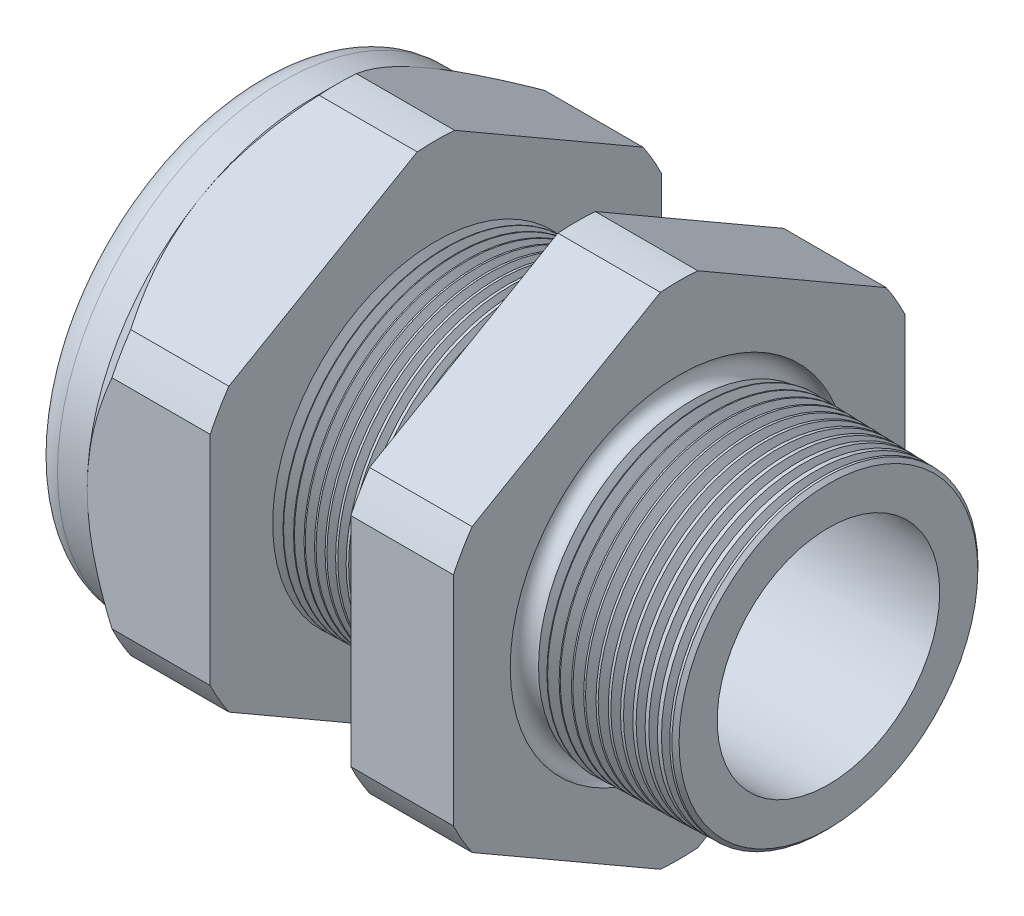
SolidWorks part; units mm, degrees
ref_plane "Front Plane" through (0, 0, 0) normal (0, 0, 1) x (1, 0, 0)
ref_plane "Top Plane" through (0, 0, 0) normal (0, 1, 0) x (1, 0, 0)
ref_plane "Right Plane" through (0, 0, 0) normal (1, 0, 0) x (0, 0, -1)
sketch "Sketch10" plane through (0, 0, 0) normal (0, 0, 1) x (1, 0, 0)
  line L0 (0, 0) -> (-115.3565, 0) construction
  line L1 (-38.862, 9.017) -> (-25.662, 9.017)
  line L2 (3.048, 8.1382) -> (3.048, 11.1862)
  line L3 (-7.874, 11.4722) -> (3.048, 11.1862)
  line L4 (-7.874, 33.02) -> (-7.874, 11.4722)
  line L5 (-7.874, 33.02) -> (-15.374, 33.02)
  line L6 (-15.374, 33.02) -> (-15.374, 11.6686)
  line L7 (-25.662, 11.938) -> (-15.374, 11.6686)
  line L8 (-25.662, 11.938) -> (-25.662, 33.02)
  line L9 (-25.662, 33.02) -> (-34.662, 33.02)
  line L10 (-34.662, 33.02) -> (-34.662, 16.51)
  line L11 (-34.662, 16.51) -> (-38.862, 16.51)
  line L12 (-38.862, 16.51) -> (-38.862, 9.017)
  line L13 (-25.662, 9.017) -> (3.048, 8.1382)
  dimension "D1" = 41.91
  dimension "D2" = 18.034
  dimension "D3" = 1.5
  dimension "D4" = 3.048
  dimension "A" = 23.876
  dimension "D6" = 33.02
  dimension "D8" = 66.04
  dimension "D9" = 4.2
  dimension "D10" = 9
  dimension "D11" = 7.5
  dimension "D" = 10.922
revolve "Revolve2" add sketch "Sketch10" angle 360 about L0
sketch "Sketch12" plane through (-34.662, 0, 0) normal (-1, 0, 0) x (0, 0, 1)
  line L1 (-1.3666, 18.2751) -> (-15.1434, 10.3211)
  line L2 (-16.51, 7.954) -> (-16.51, -7.954)
  line L3 (-15.1434, -10.3211) -> (-1.3666, -18.2751)
  line L4 (1.3666, -18.2751) -> (15.1434, -10.3211)
  line L5 (16.51, -7.954) -> (16.51, 7.954)
  line L6 (15.1434, 10.3211) -> (1.3666, 18.2751)
  circle A0 centre (0, 0) radius 16.51 construction
  arc A1 (1.3666, 18.2751) -> (-1.3666, 18.2751) centre (0, 0) ccw
  arc A2 (-15.1434, 10.3211) -> (-16.51, 7.954) centre (0, 0) ccw
  arc A3 (-16.51, -7.954) -> (-15.1434, -10.3211) centre (0, 0) ccw
  arc A4 (-1.3666, -18.2751) -> (1.3666, -18.2751) centre (0, 0) ccw
  arc A5 (15.1434, -10.3211) -> (16.51, -7.954) centre (0, 0) ccw
  arc A6 (16.51, 7.954) -> (15.1434, 10.3211) centre (0, 0) ccw
  dimension "D2" = 36.6522
  dimension "D1" = 33.02
extrude "Cut-Extrude2" cut sketch "Sketch12" against normal through all flip side to cut
fillet "Fillet4" radius 2.032 1 edges at (-38.862, 0, -16.51)
sketch "Sketch19" plane through (-34.662, 0, 0) normal (-1, 0, 0) x (0, 0, 1)
  line L0 (16.51, 0) -> (16.51, 7.954) construction
  circle A0 centre (0, 0) radius 16.51
extrude "Cut-Extrude3" cut sketch "Sketch19" against normal blind 3.998 draft 45 flip side to cut
chamfer "Chamfer1" distance 0.254 angle 45 1 edges at (3.048, 0, -11.1862)
sketch "Sketch21" plane through (-38.862, 0, 0) normal (-1, 0, 0) x (0, 0, 1)
  circle A0 centre (0, 0) radius 9.017
  circle A2 centre (0, 0) radius 9.017 construction
extrude "plug" add sketch "Sketch21" against normal blind 8.89 separate body
sketch "Sketch22" plane through (-38.862, 0, 0) normal (-1, 0, 0) x (0, 0, 1)
  circle A0 centre (0, 0) radius 8.763
  circle A1 centre (0, 0) radius 9.017 construction
  dimension "D1" = 0.254
extrude "Cut-Extrude4" cut sketch "Sketch22" against normal blind 0.508
sketch "Sketch27" plane through (-38.354, 0, 0) normal (-1, 0, 0) x (0, 0, 1)
  line L0 (-4.3624, 0) -> (4.3624, 0) construction
  circle A0 centre (-5.0653, 0) radius 3.683
  circle A1 centre (0, 0) radius 8.763 construction
  dimension "D1" = 0.0147
  dimension "holedia" = 7.366
extrude "plugholes" cut sketch "Sketch27" against normal through all
pattern_circular "CirPattern1" count 2 over 360 about axis through (0, 0, 0) along (1, 0, 0) of "plugholes"
sketch "Sketch28" [suppressed] plane through (-38.354, 0, 0) normal (-1, 0, 0) x (0, 0, 1)
  circle A0 centre (0, 0) radius 1.905
  dimension "midholedia" = 7.366
extrude "midhole" [suppressed] cut sketch "Sketch28" against normal through all
sketch "Sketch29" plane through (0, 0, 0) normal (0, 0, 1) x (1, 0, 0)
  line L0 (-25.662, 11.938) -> (-24.929, 11.9188)
  line L1 (-15.374, 11.6686) -> (-25.662, 11.938) construction
  line L2 (-24.929, 11.9188) -> (-25.3121, 11.2936)
  line L3 (-25.3121, 11.2936) -> (-25.662, 11.938)
  dimension "D1" = 60
  dimension "D2" = 60
  dimension "D3" = 0.635
revolve "Cut-Revolve1" cut sketch "Sketch29" angle 360 about axis through (0, 0, 0) along (-1, 0, 0)
pattern_linear "LPattern1" count 14 spacing 0.762 along (1, 0, 0) of "Cut-Revolve1"
sketch "Sketch30" plane through (0, 0, 0) normal (0, 0, 1) x (1, 0, 0)
  line L0 (-7.874, 11.4722) -> (-6.9944, 11.4492)
  line L1 (-7.874, 18.2751) -> (-7.874, 10.3211) construction
  line L2 (2.7941, 11.1929) -> (-7.874, 11.4722) construction
  line L3 (-6.9944, 11.4492) -> (-7.4542, 10.6989)
  line L4 (-7.4542, 10.6989) -> (-7.874, 11.4722)
  dimension "D1" = 60
  dimension "D2" = 60
  dimension "D3" = 0.762
revolve "Cut-Revolve2" cut sketch "Sketch30" angle 360 about axis through (0, 0, 0) along (-1, 0, 0)
pattern_linear "LPattern2" count 12 spacing 0.889 along (1, 0, 0) of "Cut-Revolve2"
sketch "Sketch31" [suppressed] plane through (-38.354, 0, 0) normal (-1, 0, 0) x (0, 0, 1)
  line L0 (-1.905, 1.905) -> (1.905, 1.905)
  line L1 (-1.905, -1.905) -> (1.905, -1.905)
  circle A0 centre (0, 0) radius 1.905 construction
  arc A1 (-1.905, 1.905) -> (-1.905, -1.905) centre (-1.905, 0) ccw
  arc A2 (1.905, 1.905) -> (1.905, -1.905) centre (1.905, 0) cw
extrude "Cut-Extrude5" [suppressed] cut sketch "Sketch31" against normal through all
sketch "Sketch32" plane through (0, 0, 0) normal (0, 0, 1) x (1, 0, 0)
  line L0 (-7.874, 18.2751) -> (-7.874, 10.3211) construction
  circle A0 centre (-7.747, 11.4722) radius 0.889
  dimension "D2" = 1.778
  dimension "D1" = 0.127
revolve "Cut-Revolve3" cut sketch "Sketch32" angle 360 about axis through (0, 0, 0) along (-1, 0, 0)
